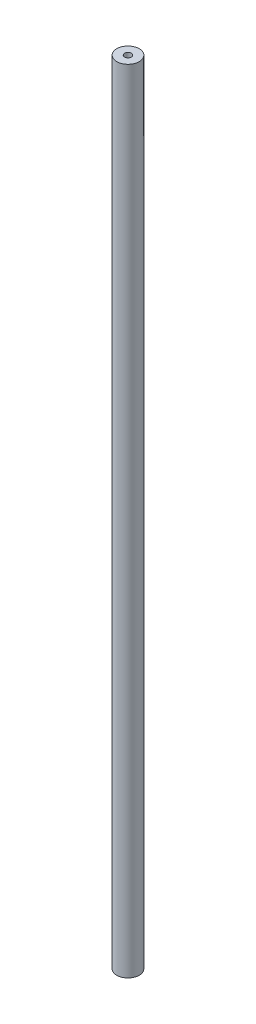
SolidWorks part; units mm, degrees
ref_plane "Front Plane" through (0, 0, 0) normal (0, 0, 1) x (1, 0, 0)
ref_plane "Top Plane" through (0, 0, 0) normal (0, 1, 0) x (1, 0, 0)
ref_plane "Right Plane" through (0, 0, 0) normal (1, 0, 0) x (0, 0, -1)
sketch "Sketch1" plane through (0, 0, 0) normal (0, 1, 0) x (1, 0, 0)
  circle A0 centre (0, 0) radius 5
  dimension "D1" = 10
extrude "Boss-Extrude1" add sketch "Sketch1" along normal blind 353 contours A0
sketch "Sketch2" plane through (0, 353, 0) normal (0, 1, 0) x (1, 0, 0)
  circle A0 centre (0, 0) radius 1.5
  dimension "D1" = 3
extrude "Cut-Extrude1" cut sketch "Sketch2" against normal blind 10
